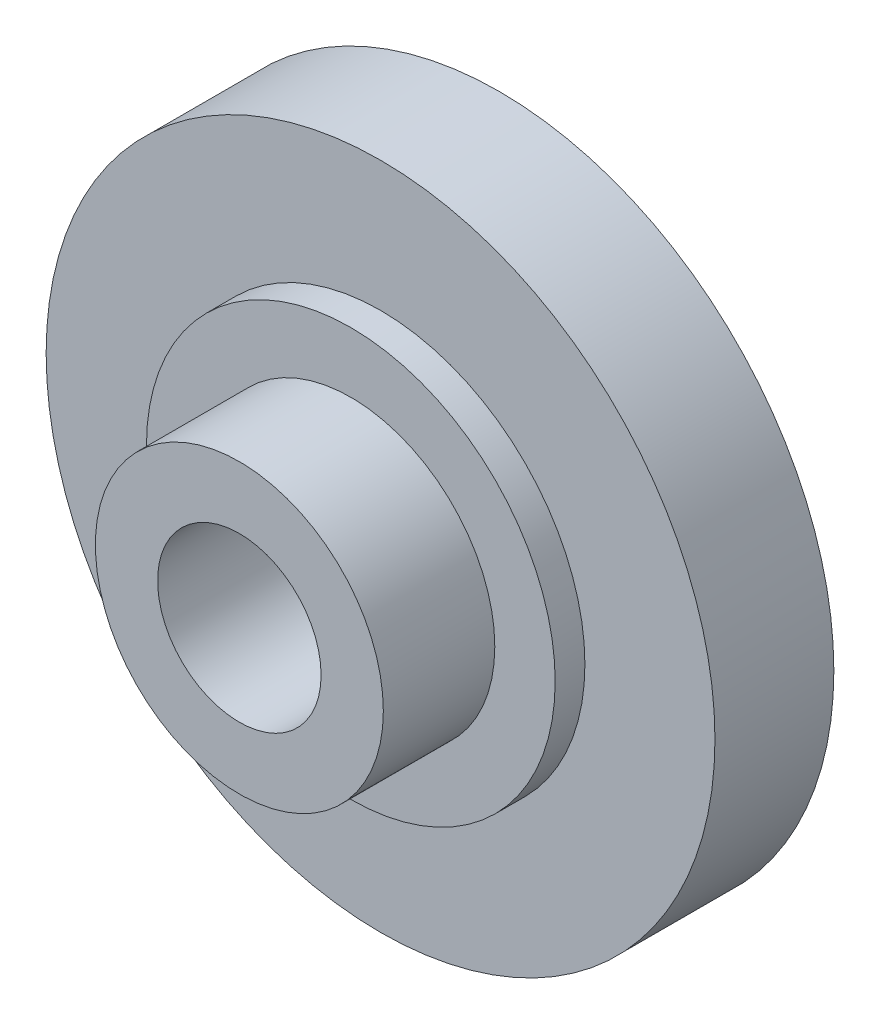
SolidWorks part; units mm, degrees
ref_plane "Front Plane" through (0, 0, 0) normal (0, 0, 1) x (1, 0, 0)
ref_plane "Top Plane" through (0, 0, 0) normal (0, 1, 0) x (1, 0, 0)
ref_plane "Right Plane" through (0, 0, 0) normal (1, 0, 0) x (0, 0, -1)
sketch "Sketch1" plane through (0, 0, 0) normal (0, 0, 1) x (1, 0, 0)
  circle A0 centre (0, 0) radius 9
  circle A1 centre (0, 0) radius 2.2
extrude "Boss-Extrude1" add sketch "Sketch1" along normal blind 7
sketch "Sketch2" plane through (0, 0, 7) normal (0, 0, 1) x (1, 0, 0)
  circle A0 centre (0, 0) radius 5.5
  circle A1 centre (0, 0) radius 9 construction
  circle A2 centre (0, 0) radius 9
extrude "Cut-Extrude1" cut sketch "Sketch2" against normal blind 3.8
sketch "Sketch3" plane through (0, 0, 7) normal (0, 0, 1) x (1, 0, 0)
  circle A0 centre (0, 0) radius 3.875
  circle A1 centre (0, 0) radius 5.5 construction
  circle A2 centre (0, 0) radius 5.5
extrude "Cut-Extrude2" cut sketch "Sketch3" against normal blind 3
